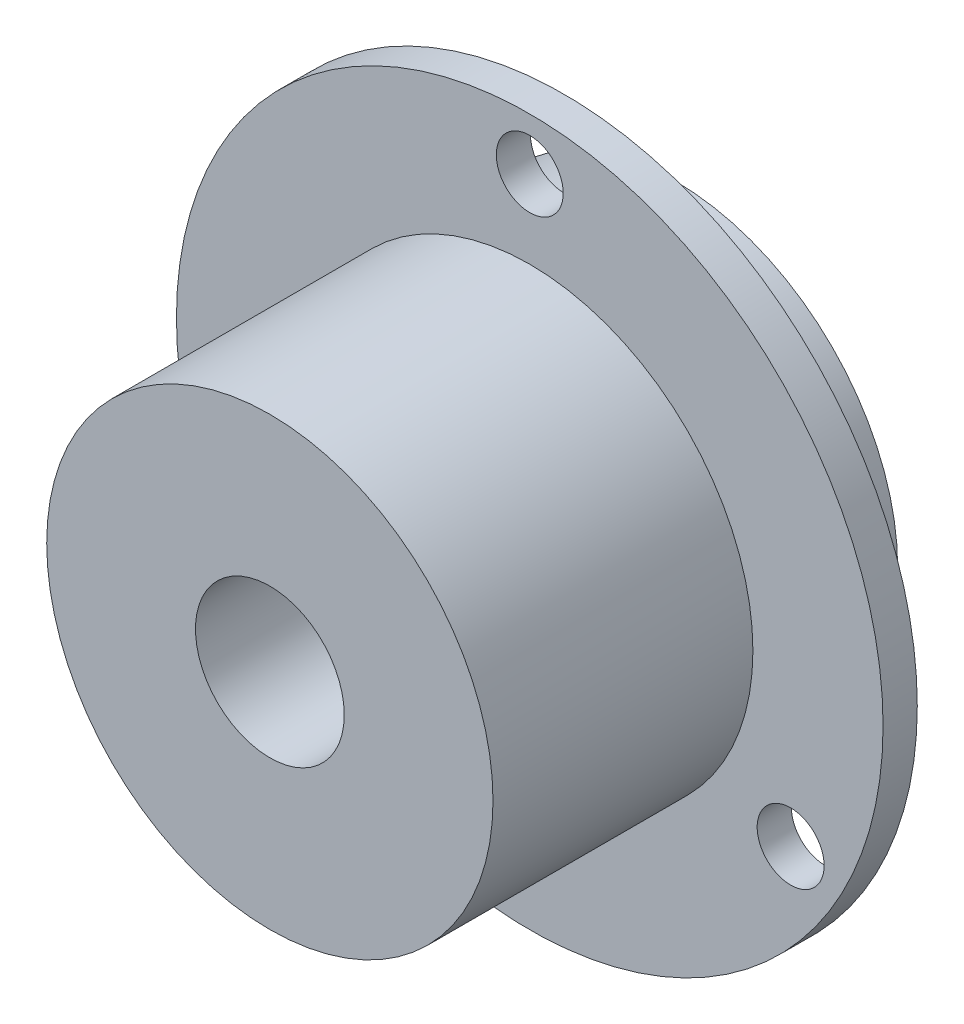
SolidWorks part; units mm, degrees
material "ABS"
ref_plane "Front Plane" through (0, 0, 0) normal (0, 0, 1) x (1, 0, 0)
ref_plane "Top Plane" through (0, 0, 0) normal (0, 1, 0) x (1, 0, 0)
ref_plane "Right Plane" through (0, 0, 0) normal (1, 0, 0) x (0, 0, -1)
sketch "Sketch2" plane through (0, 0, 0) normal (0, 1, 0) x (1, 0, 0)
  line L0 (5, -17.47) -> (5, 9.73)
  line L1 (5, 9.73) -> (15, 9.73)
  line L2 (15, 9.73) -> (15, 2.3)
  line L3 (15, 2.3) -> (23.75, 2.3)
  line L4 (23.75, 2.3) -> (23.75, 0)
  line L5 (23.75, 0) -> (15, 0)
  line L6 (15, 0) -> (15, -17.47)
  line L7 (15, -17.47) -> (5, -17.47)
  line L8 (0, -39.285) -> (0, 36.5274) construction
  dimension "D1" = 27.2
  dimension "D2" = 30
  dimension "D3" = 10
  dimension "D4" = 30
  dimension "D5" = 2.3
  dimension "D6" = 47.5
  dimension "D7" = 7.43
revolve "Revolve1" add sketch "Sketch2" angle 360 about L8
sketch "Sketch3" plane through (0, 0, 0) normal (0, 0, 1) x (1, 0, 0)
  circle A0 centre (0, 0) radius 20.25 construction
  circle A1 centre (0, 20.25) radius 2.25
  circle A2 centre (17.537, -10.125) radius 2.25
  circle A3 centre (-17.537, -10.125) radius 2.25
  point P12 (0, 0)
  dimension "D1" = 40.5
  dimension "D2" = 4.5
  dimension "D3" = 3
extrude "Cut-Extrude1" cut sketch "Sketch3" against normal mid plane 10
